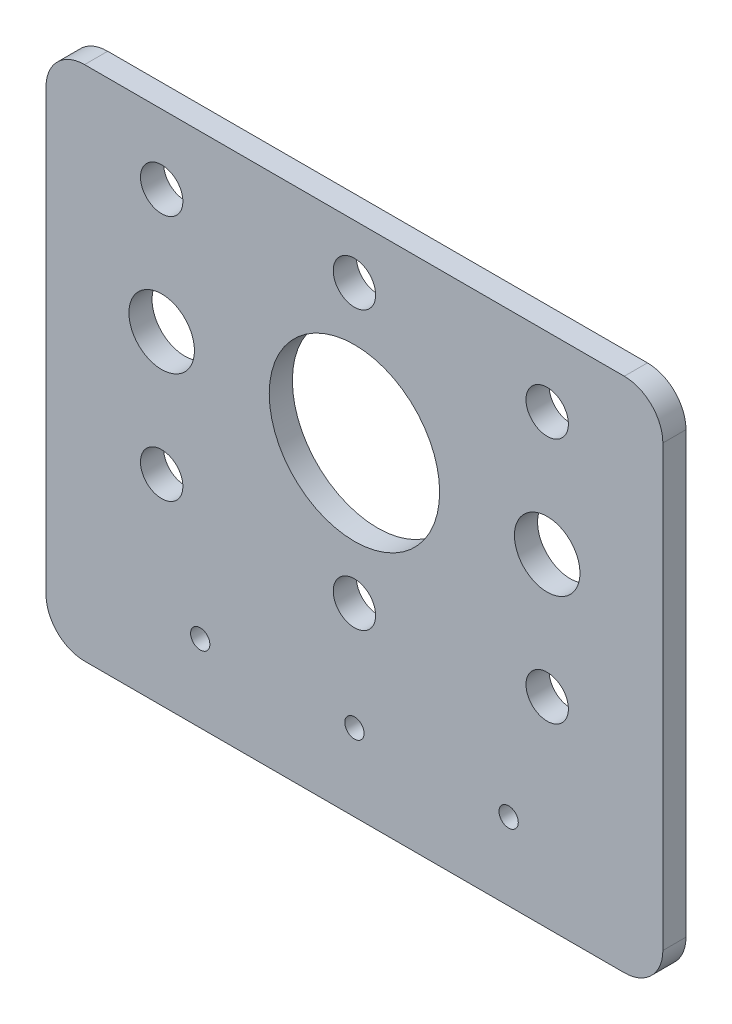
SolidWorks part; units mm, degrees
ref_plane "前视基准面" through (0, 0, 0) normal (0, 0, 1) x (1, 0, 0)
ref_plane "上视基准面" through (0, 0, 0) normal (0, 1, 0) x (1, 0, 0)
ref_plane "右视基准面" through (0, 0, 0) normal (1, 0, 0) x (0, 0, -1)
sketch "草图1" plane through (0, 0, 0) normal (0, 0, 1) x (1, 0, 0)
  line L0 (-73.587, 0) -> (88.4753, 0) construction
  line L1 (0, 53.9394) -> (0, -52.9631) construction
  line L2 (-73.587, -15.5) -> (88.4753, -15.5) construction
  line L3 (-15.5, 53.9394) -> (-15.5, -52.9631) construction
  line L4 (-73.587, 15.5) -> (88.4753, 15.5) construction
  line L5 (15.5, 53.9394) -> (15.5, -52.9631) construction
  line L6 (-25, 53.9394) -> (-25, -52.9631) construction
  line L7 (25, 53.9394) -> (25, -52.9631) construction
  line L8 (-73.587, -16) -> (88.4753, -16) construction
  line L9 (-73.587, 16) -> (88.4753, 16) construction
  line L10 (-73.587, -32) -> (88.4753, -32) construction
  line L11 (-20, 53.9394) -> (-20, -52.9631) construction
  line L12 (20, 53.9394) -> (20, -52.9631) construction
  line L13 (-40, 20) -> (-40, -37)
  line L14 (40, 20) -> (40, -37)
  line L15 (-35, -42) -> (35, -42)
  line L16 (-35, 25) -> (35, 25)
  line L17 (-40, 53.9394) -> (-40, -52.9631) construction
  line L18 (-73.587, -42) -> (88.4753, -42) construction
  line L19 (40, 53.9394) -> (40, -52.9631) construction
  line L20 (-73.587, 25) -> (88.4753, 25) construction
  line L21 (-73.587, -18) -> (88.4753, -18) construction
  line L22 (-73.587, 18) -> (88.4753, 18) construction
  circle A0 centre (0, 0) radius 11.05
  circle A5 centre (-25, 16) radius 2.75
  circle A6 centre (-25, -16) radius 2.75
  circle A7 centre (25, -16) radius 2.75
  circle A8 centre (25, 16) radius 2.75
  circle A9 centre (0, -32) radius 1.25
  circle A10 centre (-20, -32) radius 1.25
  circle A11 centre (20, -32) radius 1.25
  circle A12 centre (-25, 0) radius 4.25
  circle A13 centre (25, 0) radius 4.25
  arc A14 (-40, -37) -> (-35, -42) centre (-35, -37) ccw
  arc A15 (35, -42) -> (40, -37) centre (35, -37) ccw
  arc A16 (40, 20) -> (35, 25) centre (35, 20) ccw
  arc A17 (-35, 25) -> (-40, 20) centre (-35, 20) ccw
  circle A18 centre (0, 18) radius 2.75
  circle A19 centre (0, -18) radius 2.75
  dimension "D1" = 22.1
  dimension "D4" = 18
  dimension "D10" = 5.5
  dimension "D11" = 5.5
  dimension "D15" = 2.5
  dimension "D16" = 8.5
  dimension "D21" = 5
  dimension "D22" = 5.5
  dimension "D23" = 5.5
  dimension "D2" = 15.5
  dimension "D3" = 15.5
  dimension "D6" = 25
  dimension "D7" = 25
  dimension "D8" = 16
  dimension "D9" = 16
  dimension "D12" = 32
  dimension "D13" = 20
  dimension "D14" = 20
  dimension "D17" = 40
  dimension "D18" = 40
  dimension "D19" = 10
  dimension "D20" = 67
  dimension "D5" = 18
extrude "凸台-拉伸1" add sketch "草图1" along normal blind 3
